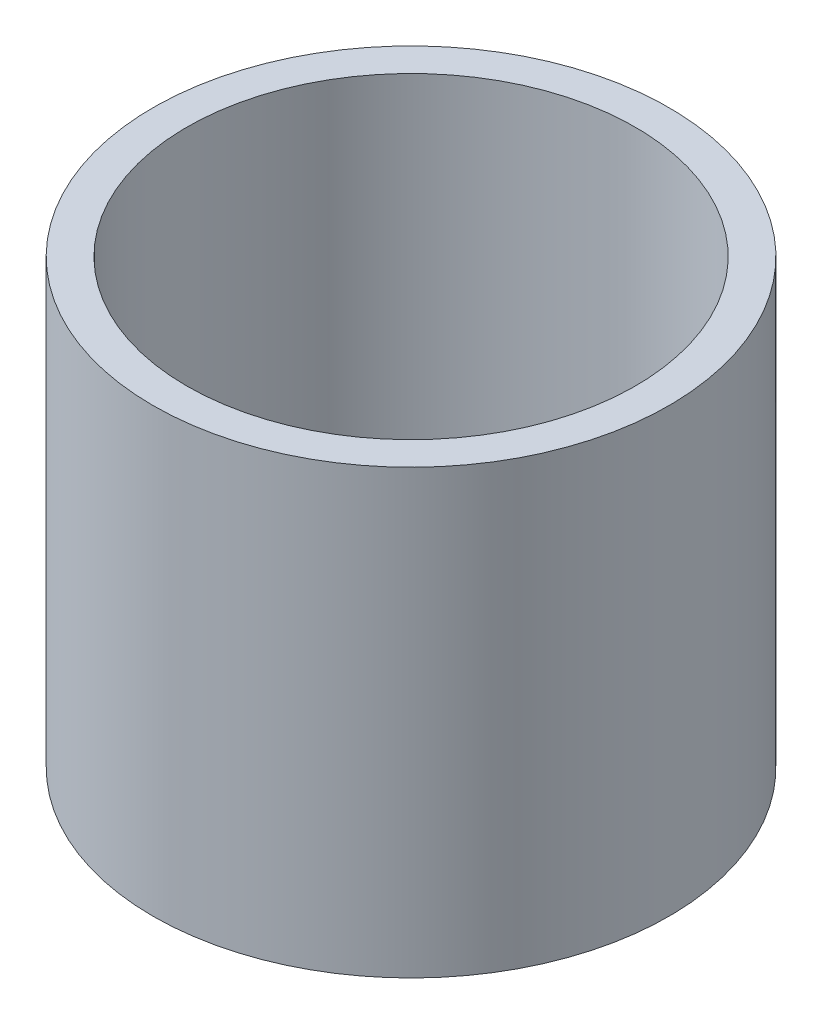
SolidWorks part; units mm, degrees
material "PVC Rigid"
ref_plane "Front Plane" through (0, 0, 0) normal (0, 0, 1) x (1, 0, 0)
ref_plane "Top Plane" through (0, 0, 0) normal (0, 1, 0) x (1, 0, 0)
ref_plane "Right Plane" through (0, 0, 0) normal (1, 0, 0) x (0, 0, -1)
sketch "Sketch2" plane through (0, 0, 0) normal (0, 1, 0) x (1, 0, 0)
  circle A0 centre (0, 0) radius 44.45
  circle A1 centre (0, 0) radius 38.6334
  dimension "D1" = 88.9
  dimension "D2" = 77.2668
extrude "Boss-Extrude1" add sketch "Sketch2" along normal blind 76.2
